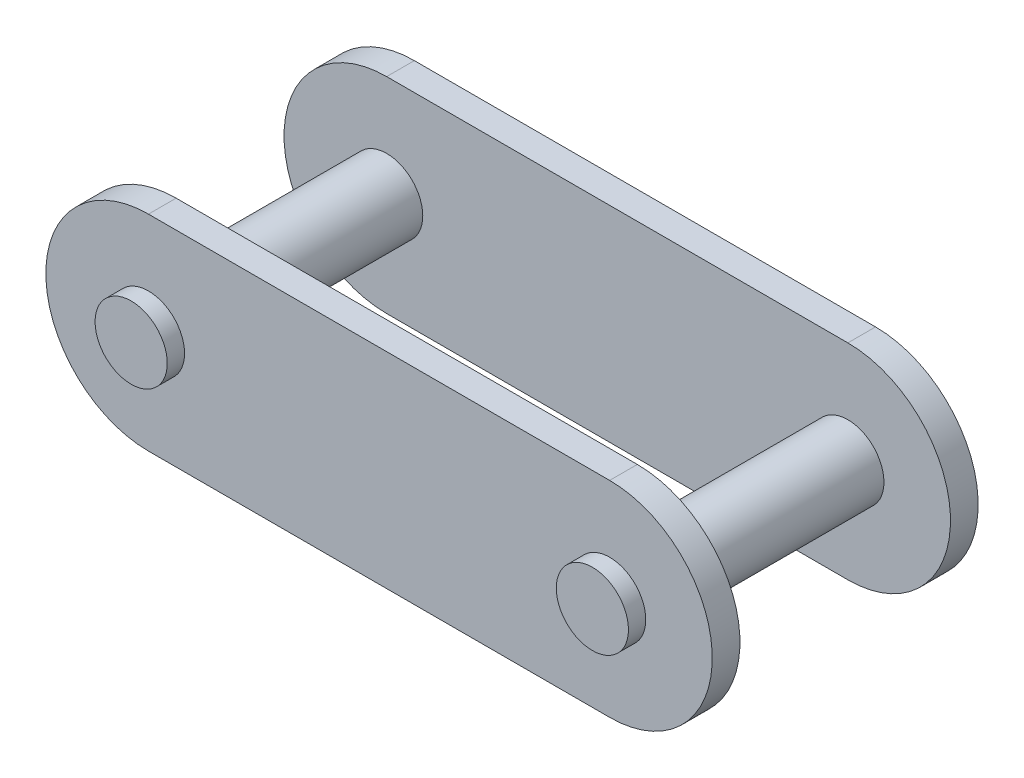
SolidWorks part; units mm, degrees
ref_plane "Front Plane" through (0, 0, 0) normal (0, 0, 1) x (1, 0, 0)
ref_plane "Top Plane" through (0, 0, 0) normal (0, 1, 0) x (1, 0, 0)
ref_plane "Right Plane" through (0, 0, 0) normal (1, 0, 0) x (0, 0, -1)
sketch "Sketch1" plane through (0, 0, 0) normal (0, 0, 1) x (1, 0, 0)
  line L0 (-12.7, 0) -> (12.7, 0) construction
  line L1 (-12.7, 5.6515) -> (12.7, 5.6515)
  line L2 (-12.7, -5.6515) -> (12.7, -5.6515)
  arc A0 (-12.7, 5.6515) -> (-12.7, -5.6515) centre (-12.7, 0) ccw
  arc A1 (12.7, -5.6515) -> (12.7, 5.6515) centre (12.7, 0) ccw
  circle A2 centre (-12.7, 0) radius 1.9875
  circle A3 centre (12.7, 0) radius 1.9875
  point P2 (0, 0)
  dimension "D2" = 25.4
  dimension "D3" = 3.9751
  dimension "D1" = 11.303
extrude "Boss-Extrude1" add sketch "Sketch1" along normal blind 1.524
ref_plane "Plane1" through (0, 0, -5.7975) normal (0, 0, 1) x (1, 0, 0)
sketch "Sketch3" plane through (0, 0, 0) normal (0, 0, -1) x (-1, 0, 0)
  circle A2 centre (-12.7, 0) radius 1.9875 construction
  circle A3 centre (12.7, 0) radius 1.9875 construction
  circle A4 centre (-12.7, 0) radius 1.9875
  circle A5 centre (12.7, 0) radius 1.9875
extrude "Boss-Extrude2" add sketch "Sketch3" along normal up to surface (8.274 mm away) from offset 2.4765
mirror "Mirror4" about plane through (0, 0, -5.7975) normal (0, 0, 1) of "Boss-Extrude2", "Boss-Extrude1"
